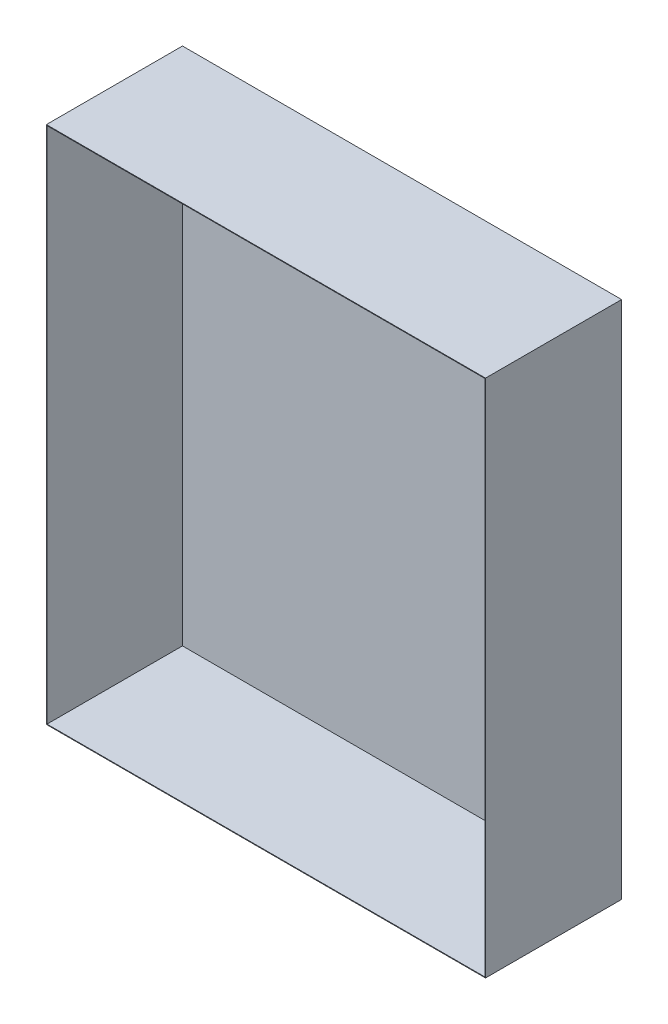
SolidWorks part; units mm, degrees
ref_plane "Front Plane" through (0, 0, 0) normal (0, 0, 1) x (1, 0, 0)
ref_plane "Top Plane" through (0, 0, 0) normal (0, 1, 0) x (1, 0, 0)
ref_plane "Right Plane" through (0, 0, 0) normal (1, 0, 0) x (0, 0, -1)
sketch "Sketch1" plane through (0, 0, 0) normal (0, 1, 0) x (1, 0, 0)
  line L1 (-901.7, -279.4) -> (901.7, -279.4)
  line L2 (-901.7, -279.4) -> (-901.7, 279.4)
  line L3 (-901.7, 279.4) -> (901.7, 279.4)
  line L4 (901.7, -279.4) -> (901.7, 279.4)
  line L5 (-901.7, -279.4) -> (901.7, 279.4) construction
  line L6 (-901.7, 279.4) -> (901.7, -279.4) construction
  point P0 (0, 0)
  dimension "D1" = 558.8
  dimension "D2" = 1803.4
extrude "Boss-Extrude1" add sketch "Sketch1" along normal blind 2133.6
shell "Shell1" thickness 2.54
